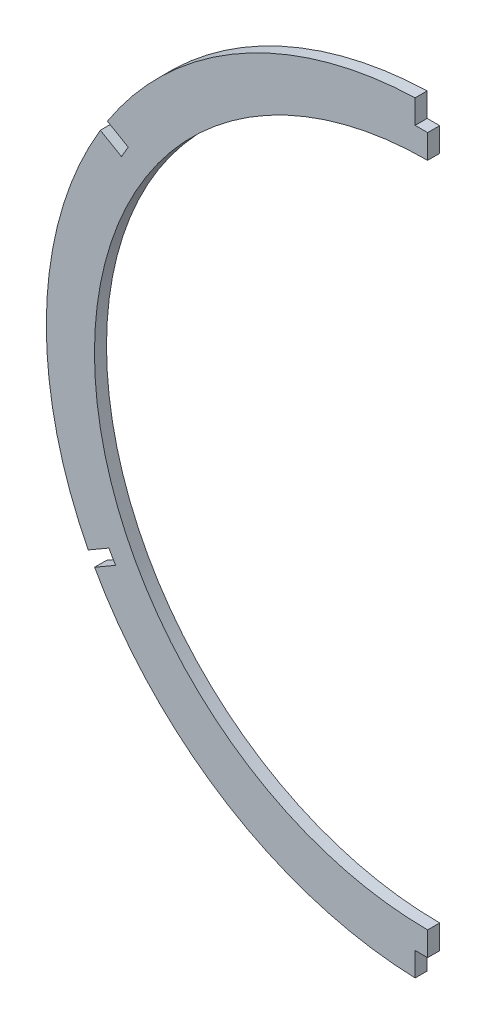
SolidWorks part; units mm, degrees
material "Plywood"
ref_plane "Front Plane" through (0, 0, 0) normal (0, 0, 1) x (1, 0, 0)
ref_plane "Top Plane" through (0, 0, 0) normal (0, 1, 0) x (1, 0, 0)
ref_plane "Right Plane" through (0, 0, 0) normal (1, 0, 0) x (0, 0, -1)
sketch "Sketch2" plane through (0, 0, 0) normal (0, 0, 1) x (1, 0, 0)
  line L0 (0, 0) -> (0, 240.9936) construction
  line L1 (-1.7839, 106.6642) -> (-1.7839, 99.822) construction
  line L2 (1.7839, 106.6642) -> (1.7839, 99.822) construction
  line L3 (-1.7839, 99.822) -> (1.7839, 99.822) construction
  line L4 (-87.7705, -42.8471) -> (-87.8712, -42.9053) construction
  line L5 (-604.1774, -338.907) -> (0, 9.8743) construction
  line L6 (-89.5483, -39.7674) -> (-83.8289, -36.4657) construction
  line L7 (-87.7705, -42.8471) -> (-82.0511, -39.5454) construction
  line L8 (-83.8289, -36.4657) -> (-82.0511, -39.5454) construction
  line L9 (604.1774, -338.907) -> (0, 9.8743) construction
  line L10 (87.7705, -42.8471) -> (82.0511, -39.5454) construction
  line L11 (87.7705, -42.8471) -> (87.8712, -42.9053) construction
  line L12 (89.5483, -39.7674) -> (83.8289, -36.4657) construction
  line L13 (83.8289, -36.4657) -> (82.0511, -39.5454) construction
  arc A0 (-7.652, 93.6463) -> (7.652, 93.6463) centre (0, 6.0782) ccw
  arc A1 (-1.7839, 106.6642) -> (-89.5483, -39.7674) centre (0, 6.0782) ccw
  arc A6 (-1.778, 93.962) -> (-7.652, 93.6463) centre (0, 6.0782) ccw
  circle A7 centre (0, 6.0782) radius 87.9018 construction
  arc A8 (0, 93.98) -> (-1.778, 93.962) centre (0, 6.0782) ccw
  arc A9 (1.778, 93.962) -> (0, 93.98) centre (0, 6.0782) ccw
  arc A10 (1.778, 93.962) -> (0, 93.98) centre (0, 6.0782) ccw construction
  arc A12 (7.652, 93.6463) -> (1.778, 93.962) centre (0, 6.0782) ccw
  arc A13 (0, 93.98) -> (-1.778, 93.962) centre (0, 6.0782) ccw construction
  arc A15 (7.652, 93.6463) -> (1.778, 93.962) centre (0, 6.0782) ccw construction
  arc A16 (-1.778, 93.962) -> (-7.652, 93.6463) centre (0, 6.0782) ccw construction
  arc A17 (0, 106.68) -> (-1.7839, 106.6642) centre (0, 6.0782) ccw
  circle A18 centre (0, 6.0782) radius 100.6018 construction
  arc A19 (1.7839, 106.6642) -> (0, 106.68) centre (0, 6.0782) ccw
  arc A20 (-87.8712, -42.9053) -> (87.8712, -42.9053) centre (0, 6.0782) ccw
  arc A21 (-89.5483, -39.7674) -> (-88.7234, -41.3442) centre (0, 6.0782) ccw
  arc A22 (-88.7234, -41.3442) -> (-87.8712, -42.9053) centre (0, 6.0782) ccw
  arc A23 (87.8712, -42.9053) -> (88.7234, -41.3442) centre (0, 6.0782) ccw
  arc A24 (89.5483, -39.7674) -> (1.7839, 106.6642) centre (0, 6.0782) ccw
  arc A25 (88.7234, -41.3442) -> (89.5483, -39.7674) centre (0, 6.0782) ccw
  point P25 (0, 99.822)
  dimension "D3" = 119.997
  dimension "D8" = 12.7
  dimension "D6" = 87.9018
  dimension "D2" = 1.7839
  dimension "D4" = 9.8743
  dimension "D5" = 3.556
  dimension "D1" = 93.98
  dimension "D7" = 5.842
  dimension "D9" = 6.604
  dimension "D10" = 3.556
extrude "Boss-Extrude1" add sketch "Sketch2" against normal blind 3.175
sketch "Sketch3" plane through (0, 0, 0) normal (1, 0, 0) x (0, 0, -1)
  line L5 (-72.4915, 152.7087) -> (76.812, 152.7087)
  line L6 (-72.4915, 152.7087) -> (-72.4915, -135.9702)
  line L7 (-72.4915, -135.9702) -> (76.812, -135.9702)
  line L8 (76.812, 152.7087) -> (76.812, -135.9702)
extrude "Cut-Extrude1" cut sketch "Sketch3" along normal through all
sketch "Sketch4" plane through (0, 0, 0) normal (0, 0, 1) x (1, 0, 0)
  line L0 (-88.1091, 62.7761) -> (-78.9966, 57.515)
  line L3 (-89.8744, 59.7185) -> (-88.1091, 62.7761)
  line L4 (0, 9.8679) -> (0, -96.8576) construction
  line L5 (0, 0) -> (0, 151.9186) construction
  line L6 (-88.9918, 61.2473) -> (-79.8792, 55.9862) construction
  line L7 (-89.8744, 59.7185) -> (-80.7619, 54.4574)
  line L8 (-80.7619, 54.4574) -> (-78.9966, 57.515)
  line L9 (-79.8792, 55.9862) -> (0, 9.8679) construction
  line L10 (0, 9.8679) -> (-60.4839, 9.8679) construction
  line L11 (-88.9918, -41.5115) -> (-79.8792, -36.2504) construction
  line L12 (-84.095, -36.646) -> (-82.3297, -39.7036)
  line L13 (-92.2228, -41.3386) -> (-84.095, -36.646)
  line L14 (-92.2228, -41.3386) -> (-90.4575, -44.3962)
  line L15 (-90.4575, -44.3962) -> (-82.3297, -39.7036)
  line L16 (-79.8792, -36.2504) -> (0, 9.8679) construction
  line L17 (0, -88.1737) -> (-3.302, -88.1737)
  line L18 (-3.302, -88.1737) -> (-3.302, -95.6228)
  line L20 (-3.302, -95.6228) -> (0, -95.6228)
  line L21 (0, -95.6228) -> (0, -88.1737)
  line L22 (-3.302, 110.2958) -> (0, 110.2958)
  line L23 (-3.302, 110.2958) -> (-3.302, 100.33)
  line L24 (-3.302, 100.33) -> (0, 100.33)
  line L25 (0, 110.2958) -> (0, 100.33)
  point P2 (-74.38, 52.8112)
  point P12 (-83.2124, -38.1748)
  point P19 (-77.7131, -34.9998)
  point P24 (0, -81.8237)
  point P27 (0, 93.98)
  dimension "D1" = 60
  dimension "D2" = 9.8679
  dimension "D3" = 3.5306
  dimension "D4" = 85.8866
  dimension "D5" = 6.35
  dimension "D6" = 89.7354
  dimension "D7" = 6.35
  dimension "D8" = 3.5306
  dimension "D9" = 3.302
  dimension "D10" = 91.6916
  dimension "D11" = 6.35
  dimension "D12" = 84.1121
  dimension "D13" = 6.35
  dimension "D14" = 3.302
extrude "Cut-Extrude2" cut sketch "Sketch4" against normal through all
